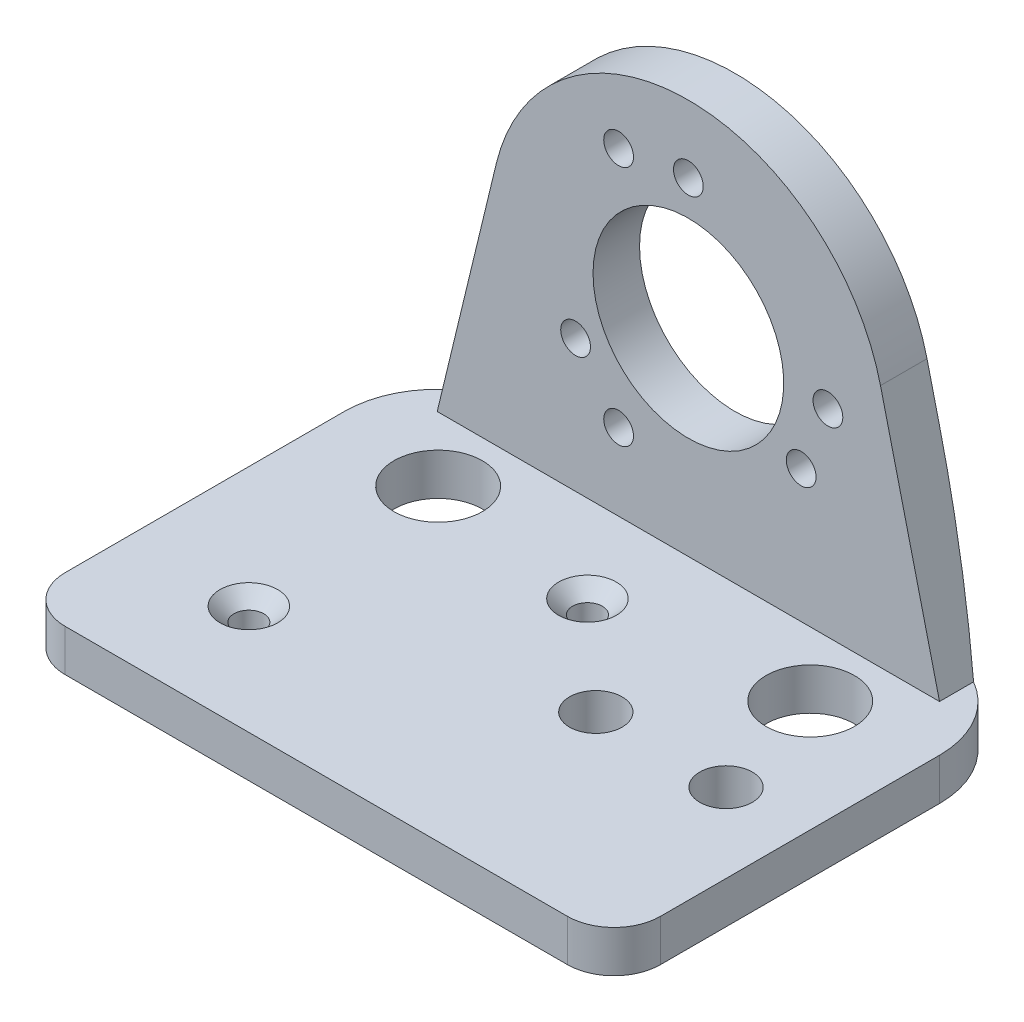
SolidWorks part; units mm, degrees
ref_plane "Front Plane" through (0, 0, 0) normal (0, 0, 1) x (1, 0, 0)
ref_plane "Top Plane" through (0, 0, 0) normal (0, 1, 0) x (1, 0, 0)
ref_plane "Right Plane" through (0, 0, 0) normal (1, 0, 0) x (0, 0, -1)
sketch "Sketch1" plane through (0, 0, 0) normal (0, 1, 0) x (1, 0, 0)
  line L0 (6.875, -1.95) -> (26.125, -1.95) construction
  line L1 (12.125, -1.95) -> (20.875, -1.95) construction
  line L2 (-32, -22.5) -> (32, -22.5)
  line L3 (32, -22.5) -> (32, 22.5)
  line L6 (-32, -22.5) -> (-32, 22.5)
  line L7 (-32, 22.5) -> (32, 22.5)
  line L9 (-32, 22.5) -> (32, -22.5) construction
  line L10 (32, 22.5) -> (-32, -22.5) construction
  line L11 (-20, 10.6) -> (0, 0) construction
  line L12 (0, 0) -> (20, 10.6) construction
  circle A0 centre (9.5, -1.95) radius 2.625 construction
  circle A1 centre (23.5, -1.95) radius 2.625 construction
  circle A2 centre (-1.5, 8.15) radius 1.6
  circle A3 centre (-19, -10.75) radius 1.6
  circle A4 centre (9.5, -1.95) radius 1.6 construction
  circle A5 centre (23.5, -1.95) radius 1.6 construction
  circle A7 centre (9.5, -1.95) radius 2.825
  circle A8 centre (23.5, -1.95) radius 2.825
  circle A9 centre (-20, 10.6) radius 4.75
  circle A10 centre (20, 10.6) radius 4.75
  point P19 (0, 0)
  point P23 (0, 0)
  dimension "D8" = 3.2
  dimension "D15" = 9.5
  dimension "D1" = 19.25
  dimension "D2" = 8.75
  dimension "D3" = 17.5
  dimension "D4" = 18.9
  dimension "D5" = 10.1
  dimension "D6" = 11
  dimension "D14" = 0.2
  dimension "D10" = 64
  dimension "D11" = 45
  dimension "D7" = 9.5
  dimension "D9" = 1.95
  dimension "D12" = 40
  dimension "D13" = 10.6
extrude "Boss-Extrude1" add sketch "Sketch1" against normal blind 4.5
chamfer "Chamfer1" distance 1.5 angle 45 2 edges at (-19, 0, 12.35) (-1.5, 0, -6.55)
sketch "Sketch2" plane through (0, 0, 0) normal (0, 0, 1) x (1, 0, 0)
  line L0 (-32, 0) -> (32, 0) construction
  line L1 (-27, 0) -> (-20.6549, 26.2438)
  line L2 (27, 0) -> (20.6549, 26.2438)
  line L3 (-27, 0) -> (-27, -4.5)
  line L4 (-27, -4.5) -> (27, -4.5)
  line L5 (27, -4.5) -> (27, 0)
  line L6 (-7.5, 34.2404) -> (0, 21.25) construction
  line L7 (0, 21.25) -> (0, 35.25) construction
  line L8 (-32, -4.5) -> (32, -4.5) construction
  line L9 (-32, -4.5) -> (-32, 0) construction
  line L10 (32, -4.5) -> (32, 0) construction
  circle A0 centre (0, 21.25) radius 19.25 construction
  arc A1 (20.6549, 26.2438) -> (-20.6549, 26.2438) centre (0, 21.25) ccw
  circle A2 centre (0, 21.25) radius 10.25
  circle A3 centre (0, 21.25) radius 15 construction
  circle A4 centre (0, 21.25) radius 14 construction
  circle A5 centre (0, 35.25) radius 1.6
  circle A6 centre (-7.5, 34.2404) radius 1.6
  circle A7 centre (12.1244, 14.25) radius 1.6
  circle A8 centre (15, 21.25) radius 1.6
  circle A9 centre (-12.1244, 14.25) radius 1.6
  circle A10 centre (-7.5, 8.2596) radius 1.6
  point P5 (0, 0)
  point P23 (0, 0)
  point P27 (0, 0)
  point P28 (0, 0)
  point P34 (0, 21.25)
  point P35 (32, -4.5)
  point P37 (32, 0)
  point P39 (-32, 0)
  point P41 (0, 0)
  point P42 (-31.7779, 7.425)
  point P43 (0, 0)
  point P44 (32, 7.425)
  point P45 (-32, -4.5)
  point P47 (0, 0)
  point P48 (0, 0)
  point P49 (-32, -4.5)
  point P51 (32, -4.5)
  point P53 (-32, 0)
  point P54 (0, 0)
  point P55 (-28.2983, -4.5)
  point P60 (0, 0)
  point P61 (28.6534, -4.5)
  dimension "D1" = 38.5
  dimension "D3" = 20.5
  dimension "D4" = 28
  dimension "D5" = 30
  dimension "D7" = 3.2
  dimension "D2" = 2
  dimension "D6" = 30
  dimension "D9" = 5
  dimension "D10" = 5
  dimension "D8" = 3
extrude "Boss-Extrude2" add sketch "Sketch2" along normal blind 5 from surface at -22.5 starting at face at (0, -2.25, -22.5)
fillet "Fillet1" radius 5 2 edges at (32, -2.25, 22.5) (-32, -2.25, 22.5)
fillet "Fillet2" radius 10 2 edges at (32, -2.25, -22.5) (-32, -2.25, -22.5)
equation "\"m3 hole\"= 3.2"
equation "\"m4 hole\"= 4.2"
equation "\"m5 hole\"= 5.2"
equation "\"m6 hole\"= 6.2"
equation "\"m8 hole\"= 8.2"
equation "\"m3 tapped\"= 2.5"
equation "\"m4 tapped\"= 3.3"
equation "\"m5 tapped\"= 4.2"
equation "\"m6 tapped\"= 5"
equation "\"m8 tapped\"= 6.8"
equation "\"D8@Sketch1\"=\"m3 hole\""
equation "\"D7@Sketch2\"=\"m3 hole\""
